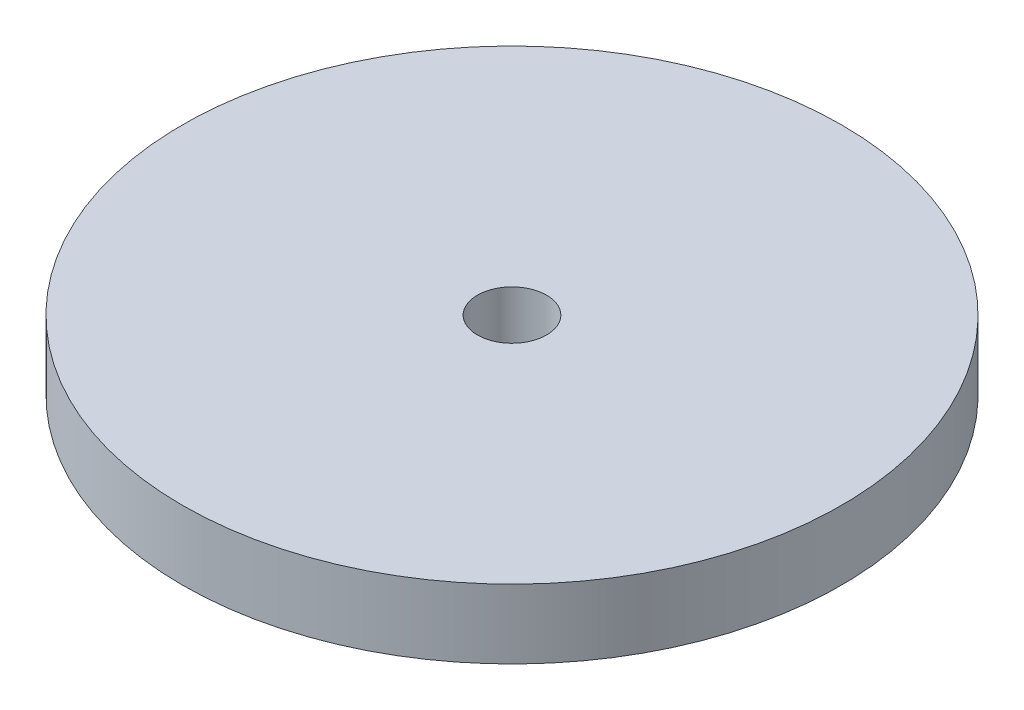
SolidWorks part; units mm, degrees
ref_plane "Front Plane" through (0, 0, 0) normal (0, 0, 1) x (1, 0, 0)
ref_plane "Top Plane" through (0, 0, 0) normal (0, 1, 0) x (1, 0, 0)
ref_plane "Right Plane" through (0, 0, 0) normal (1, 0, 0) x (0, 0, -1)
sketch "Sketch1" plane through (0, 0, 0) normal (0, 1, 0) x (1, 0, 0)
  circle A0 centre (0, 0) radius 14.3
  circle A1 centre (0, 0) radius 1.5
  dimension "D1" = 28.6
  dimension "D2" = 3
extrude "Boss-Extrude1" add sketch "Sketch1" along normal blind 3
